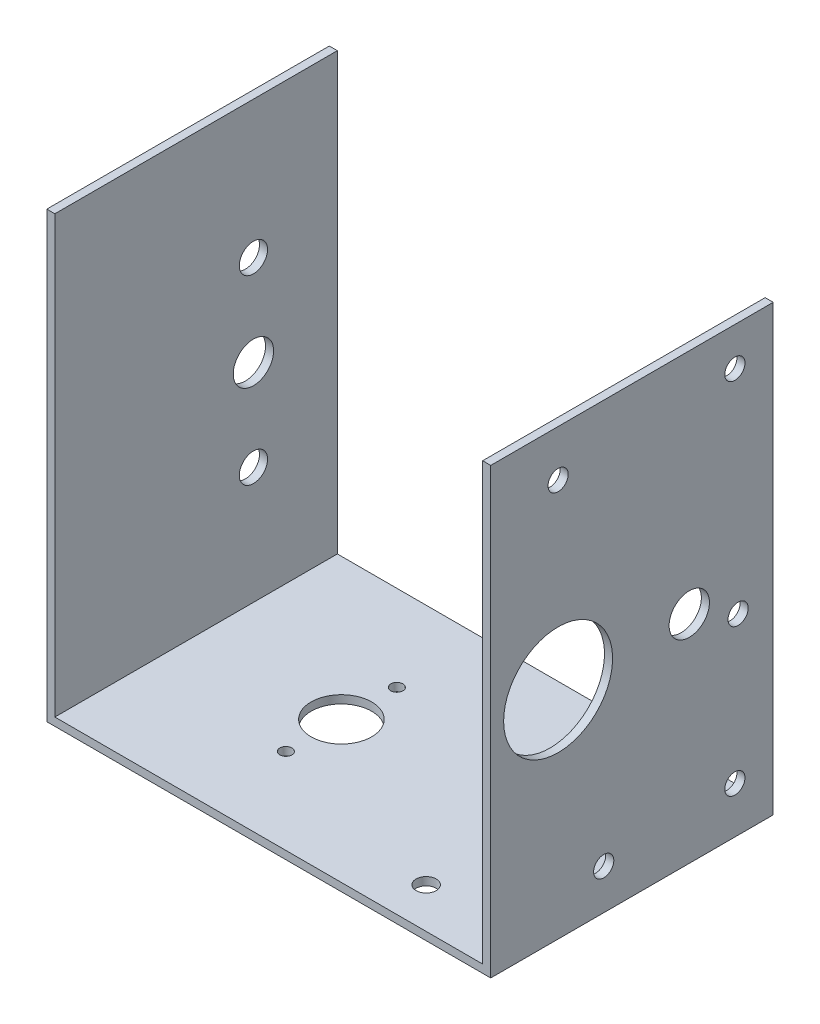
SolidWorks part; units mm, degrees
material "Liga 1060"
ref_plane "Plano frontal" through (0, 0, 0) normal (0, 0, 1) x (1, 0, 0)
ref_plane "Plano superior" through (0, 0, 0) normal (0, 1, 0) x (1, 0, 0)
ref_plane "Plano direito" through (0, 0, 0) normal (1, 0, 0) x (0, 0, -1)
sketch "Esboço1" plane through (0, 0, 0) normal (0, 1, 0) x (1, 0, 0)
  line L1 (55, -35) -> (-55, -35)
  line L2 (55, -35) -> (55, 35)
  line L3 (55, 35) -> (-55, 35)
  line L4 (-55, -35) -> (-55, 35)
  line L5 (55, -35) -> (-55, 35) construction
  line L6 (55, 35) -> (-55, -35) construction
  point P0 (0, 0)
  dimension "D1" = 110
  dimension "D2" = 70
extrude "Ressalto-extrusão1" add sketch "Esboço1" along normal blind 2
sketch "Esboço2" plane through (-55, 0, 0) normal (-1, 0, 0) x (0, 0, 1)
  line L0 (35, 2) -> (35, 0) construction
  line L1 (-35, 0) -> (35, 0)
  line L2 (-35, 0) -> (-35, 110)
  line L3 (-35, 110) -> (35, 110)
  line L4 (35, 0) -> (35, 110)
  dimension "D1" = 110
extrude "Ressalto-extrusão2" add sketch "Esboço2" against normal blind 2
sketch "Esboço3" plane through (55, 0, 0) normal (1, 0, 0) x (0, 0, -1)
  line L4 (-35, 0) -> (35, 0)
  line L5 (-35, 110) -> (-35, 0)
  line L6 (35, 110) -> (-35, 110)
  line L7 (35, 0) -> (35, 110)
  line L8 (-35, 0) -> (35, 0)
  line L9 (-35, 110) -> (-35, 0)
  line L10 (35, 110) -> (-35, 110)
  line L11 (35, 0) -> (35, 110)
  dimension "D1" = 0
extrude "Ressalto-extrusão3" add sketch "Esboço3" against normal blind 2
sketch "Esboço4" plane through (0, 2, 0) normal (0, 1, 0) x (1, 0, 0)
  line L1 (-53, -35) -> (-53, 35) construction
  line L2 (-53, -35) -> (53, -35) construction
  circle A1 centre (-17, 0) radius 7.5
  point P2 (0, 0)
  dimension "D2" = 36
  dimension "D1" = 15
  dimension "D3" = 35
extrude "Corte-extrusão1" cut sketch "Esboço4" against normal blind 6.35
sketch "Esboço5" plane through (55, 0, 0) normal (1, 0, 0) x (0, 0, -1)
  line L0 (-35, 110) -> (-35, 0) construction
  line L1 (-35, 0) -> (35, 0) construction
  circle A0 centre (-7, 10) radius 2.5
  dimension "D3" = 5
  dimension "D1" = 28
  dimension "D2" = 10
extrude "Corte-extrusão2" cut sketch "Esboço5" against normal blind 10
sketch "Esboço6" plane through (55, 0, 0) normal (1, 0, 0) x (0, 0, -1)
  circle A0 centre (-18.3, 98.5) radius 2.5 construction
  circle A1 centre (26.3, 47.5) radius 2.5 construction
  circle A2 centre (-18.3, 98.5) radius 2.5
  circle A3 centre (26.3, 47.5) radius 2.5
extrude "Corte-extrusão3" cut sketch "Esboço6" against normal blind 10
sketch "Esboço7" plane through (53, 0, 0) normal (-1, 0, 0) x (0, 0, 1)
  circle A0 centre (18.3, 53.5) radius 1 construction
  circle A1 centre (18.3, 53.5) radius 1
  circle A2 centre (18.3, 53.5) radius 13.5
  dimension "D1" = 27
extrude "Corte-extrusão5" cut sketch "Esboço7" against normal blind 10 contours A1 | A2 A1
sketch "Esboço9" plane through (55, 0, 0) normal (1, 0, 0) x (0, 0, -1)
  circle A0 centre (14.2, 53.5) radius 5
  point P2 (-18.3, 53.5)
  dimension "D2" = 10
  dimension "D1" = 32.5
extrude "Corte-extrusão6" cut sketch "Esboço9" against normal through all
sketch "Esboço10" plane through (55, 0, 0) normal (1, 0, 0) x (0, 0, -1)
  line L0 (35, 110) -> (35, 0) construction
  line L1 (-35, 0) -> (35, 0) construction
  line L2 (35, 110) -> (-35, 110) construction
  circle A2 centre (25.5, 11.5) radius 2.5
  circle A3 centre (25.5, 100.5) radius 2.5
  dimension "D5" = 5
  dimension "D6" = 5
  dimension "D1" = 9.5
  dimension "D2" = 11.5
  dimension "D3" = 9.5
  dimension "D4" = 9.5
extrude "Corte-extrusão7" cut sketch "Esboço10" against normal blind 2
sketch "Esboço11" plane through (0, 2, 0) normal (0, 1, 0) x (1, 0, 0)
  circle A0 centre (31, -25) radius 2.5 construction
  circle A1 centre (31, 25) radius 2.5 construction
  circle A2 centre (31, -25) radius 2.5
  circle A3 centre (31, 25) radius 2.5
sketch "Esboço12" plane through (-53, 0, 0) normal (1, 0, 0) x (0, 0, -1)
  line L4 (-35, 110) -> (-35, 2)
  line L5 (-35, 2) -> (35, 2)
  line L6 (35, 2) -> (35, 110)
  line L7 (35, 110) -> (-35, 110)
  line L8 (-35, 110) -> (-35, 2)
  line L9 (-35, 2) -> (35, 2)
  line L10 (35, 2) -> (35, 110)
  line L11 (35, 110) -> (-35, 110)
  circle A0 centre (14.2, 53.5) radius 5 construction
  circle A1 centre (14.2, 53.5) radius 5
  dimension "D1" = 0
extrude "Ressalto-extrusão6" [suppressed] add sketch "Esboço12" along normal blind 13.5
sketch "Esboço15" plane through (55, 0, 0) normal (1, 0, 0) x (0, 0, -1)
  circle A1 centre (-7, 10) radius 2.5
  circle A2 centre (-7, 10) radius 2.5
  circle A3 centre (26.3, 47.5) radius 2.5
  circle A4 centre (26.3, 47.5) radius 2.5
  circle A5 centre (-18.3, 98.5) radius 2.5
  circle A6 centre (-18.3, 98.5) radius 2.5
  circle A7 centre (-18.3, 53.5) radius 13.5
  circle A8 centre (-18.3, 53.5) radius 13.5
  circle A9 centre (14.2, 53.5) radius 5
  circle A10 centre (14.2, 53.5) radius 5
  circle A11 centre (25.5, 100.5) radius 2.5
  circle A12 centre (25.5, 100.5) radius 2.5
  circle A13 centre (25.5, 11.5) radius 2.5
  circle A14 centre (25.5, 11.5) radius 2.5
  circle M8 centre (25.5, 11.5) radius 2.5
  circle M9 centre (25.5, 100.5) radius 2.5
  circle M10 centre (14.2, 53.5) radius 5
  circle M11 centre (-18.3, 53.5) radius 13.5
  circle M12 centre (-18.3, 98.5) radius 2.5
  circle M13 centre (26.3, 47.5) radius 2.5
  circle M14 centre (-7, 10) radius 2.5
  line M15 (-35, 0) -> (35, 0)
  line M16 (35, 0) -> (35, 110)
  line M17 (35, 110) -> (-35, 110)
  line M18 (-35, 110) -> (-35, 0)
  dimension "D1" = 0
  dimension "D2" = 0
  dimension "D3" = 0
  dimension "D4" = 0
  dimension "D5" = 0
  dimension "D6" = 0
  dimension "D7" = 0
extrude "Ressalto-extrusão7" [suppressed] add sketch "Esboço15" along normal blind 23.5 contours M18 M15 M16 M17 M9 M11 M13 M14 M12 M10 M8
sketch "Esboço16" plane through (-55, 0, 0) normal (-1, 0, 0) x (0, 0, 1)
  line L4 (-35, 0) -> (35, 0)
  line L5 (35, 0) -> (35, 110)
  line L6 (35, 110) -> (-35, 110)
  line L7 (-35, 110) -> (-35, 0)
  line L8 (-35, 0) -> (35, 0)
  line L9 (35, 0) -> (35, 110)
  line L10 (35, 110) -> (-35, 110)
  line L11 (-35, 110) -> (-35, 0)
  dimension "D1" = 0
extrude "Corte-extrusão9" [suppressed] cut sketch "Esboço16" against normal blind 13.5
sketch "Esboço17" plane through (53, 0, 0) normal (-1, 0, 0) x (0, 0, 1)
  line L4 (-35, 2) -> (35, 2)
  line L5 (35, 2) -> (35, 110)
  line L6 (35, 110) -> (-35, 110)
  line L7 (-35, 110) -> (-35, 2)
  line L8 (-35, 2) -> (35, 2)
  line L9 (35, 2) -> (35, 110)
  line L10 (35, 110) -> (-35, 110)
  line L11 (-35, 110) -> (-35, 2)
  dimension "D1" = 0
extrude "Corte-extrusão10" [suppressed] cut sketch "Esboço17" against normal blind 23.5
sketch "Esboço18" plane through (0, 2, 0) normal (0, 1, 0) x (1, 0, 0)
  line L1 (53, 35) -> (-53, 35) construction
  line L2 (53, -35) -> (53, 35) construction
  circle A4 centre (29, 25) radius 2.5
  circle A5 centre (29, -25) radius 2.5
  dimension "D1" = 5
  dimension "D4" = 50
  dimension "D5" = 5
  dimension "D2" = 24
  dimension "D3" = 10
extrude "Corte-extrusão11" cut sketch "Esboço18" against normal up to next contours A4 | A5
sketch "Esboço19" plane through (0, 2, 0) normal (0, 1, 0) x (1, 0, 0)
  line L0 (-17, -35) -> (-17, 35) construction
  line L1 (53, 35) -> (-53, 35) construction
  line L2 (-53, -35) -> (53, -35) construction
  circle A2 centre (-17, 13.75) radius 1.5
  circle A3 centre (-17, -13.75) radius 1.5
  circle A5 centre (-17, 0) radius 7.5 construction
  point P1 (-12, 0)
  point P6 (0, 0)
  point P7 (-12, 0)
  point P13 (-12, -35)
  point P16 (0, 0)
  dimension "D2" = 3
  dimension "D3" = 3
  dimension "D1" = 13.75
  dimension "D4" = 13.75
extrude "Corte-extrusão12" cut sketch "Esboço19" against normal blind 10
sketch "Esboço20" plane through (-55, 0, 0) normal (-1, 0, 0) x (0, 0, 1)
  arc A0 (-17.7, 31) -> (-10.7, 31) centre (-14.2, 31) ccw construction
  arc A1 (-10.7, 76) -> (-17.7, 76) centre (-14.2, 76) ccw construction
  arc A2 (-17.7, 76) -> (-10.7, 76) centre (-14.2, 76) ccw construction
  arc A3 (-10.7, 31) -> (-17.7, 31) centre (-14.2, 31) ccw construction
  arc A4 (-17.7, 31) -> (-10.7, 31) centre (-14.2, 31) ccw
  arc A5 (-10.7, 31) -> (-17.7, 31) centre (-14.2, 31) ccw
  arc A6 (-17.7, 76) -> (-10.7, 76) centre (-14.2, 76) ccw
  arc A7 (-10.7, 76) -> (-17.7, 76) centre (-14.2, 76) ccw
extrude "Corte-extrusão13" cut sketch "Esboço20" against normal up to next
